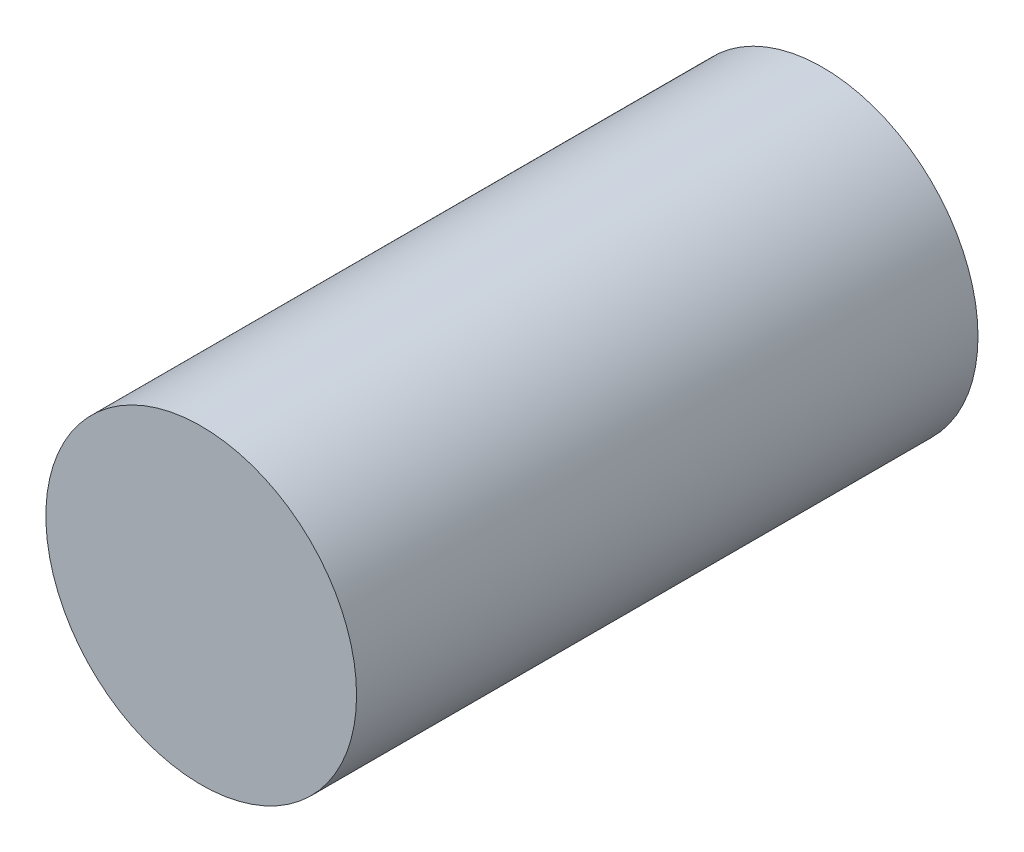
SolidWorks part; units mm, degrees
material "Nylon 101"
ref_plane "Front Plane" through (0, 0, 0) normal (0, 0, 1) x (1, 0, 0)
ref_plane "Top Plane" through (0, 0, 0) normal (0, 1, 0) x (1, 0, 0)
ref_plane "Right Plane" through (0, 0, 0) normal (1, 0, 0) x (0, 0, -1)
sketch "Sketch2" plane through (0, 0, 0) normal (0, 0, 1) x (1, 0, 0)
  circle A0 centre (0, 0) radius 5
  dimension "D1" = 10
extrude "Boss-Extrude1" add sketch "Sketch2" along normal blind 20
